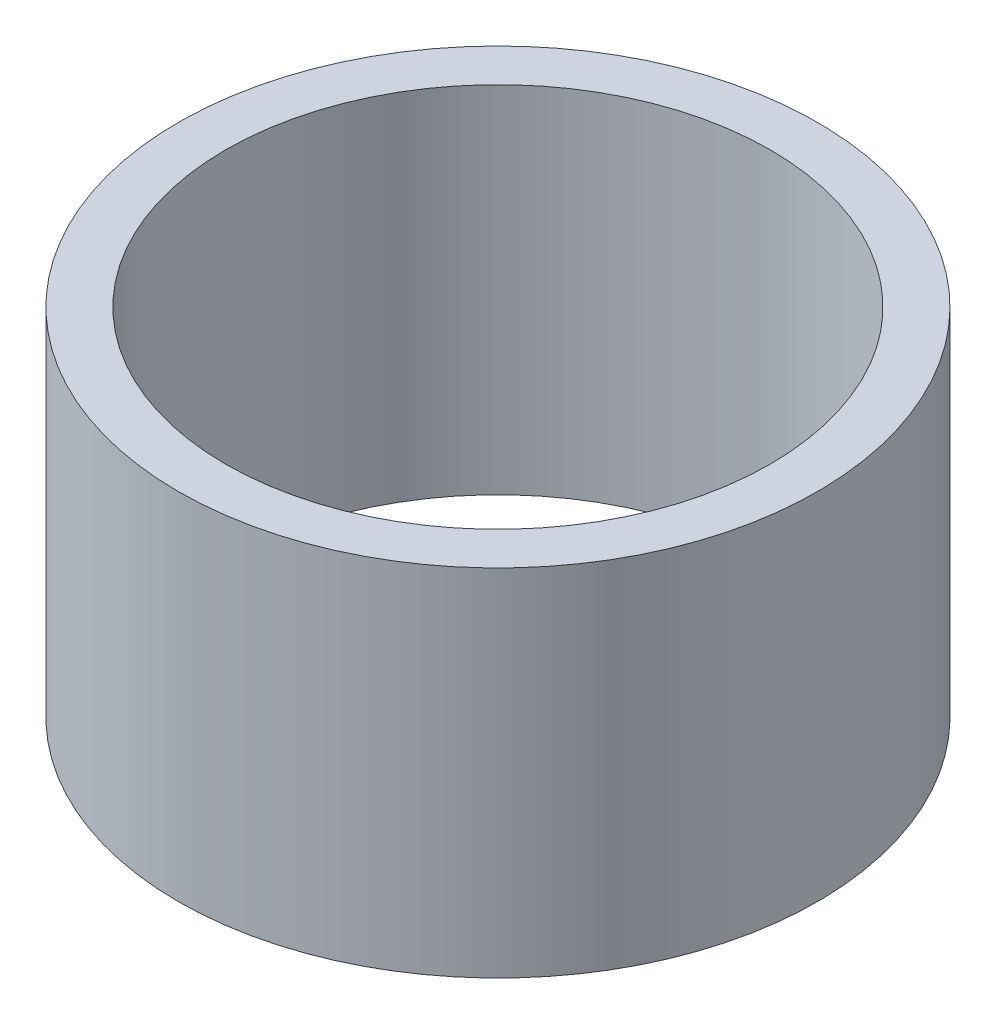
SolidWorks part; units mm, degrees
ref_plane "Front Plane" through (0, 0, 0) normal (0, 0, 1) x (1, 0, 0)
ref_plane "Top Plane" through (0, 0, 0) normal (0, 1, 0) x (1, 0, 0)
ref_plane "Right Plane" through (0, 0, 0) normal (1, 0, 0) x (0, 0, -1)
sketch "Sketch1" plane through (0, 0, 0) normal (0, 1, 0) x (1, 0, 0)
  circle A0 centre (0, 0) radius 1.35
  dimension "D1" = 2.7
extrude "Boss-Extrude1" add sketch "Sketch1" along normal blind 1.5
sketch "Sketch2" plane through (0, 1.5, 0) normal (0, 1, 0) x (1, 0, 0)
  circle A0 centre (0, 0) radius 1.15
  dimension "D1" = 2.3
extrude "Cut-Extrude1" cut sketch "Sketch2" against normal through all
